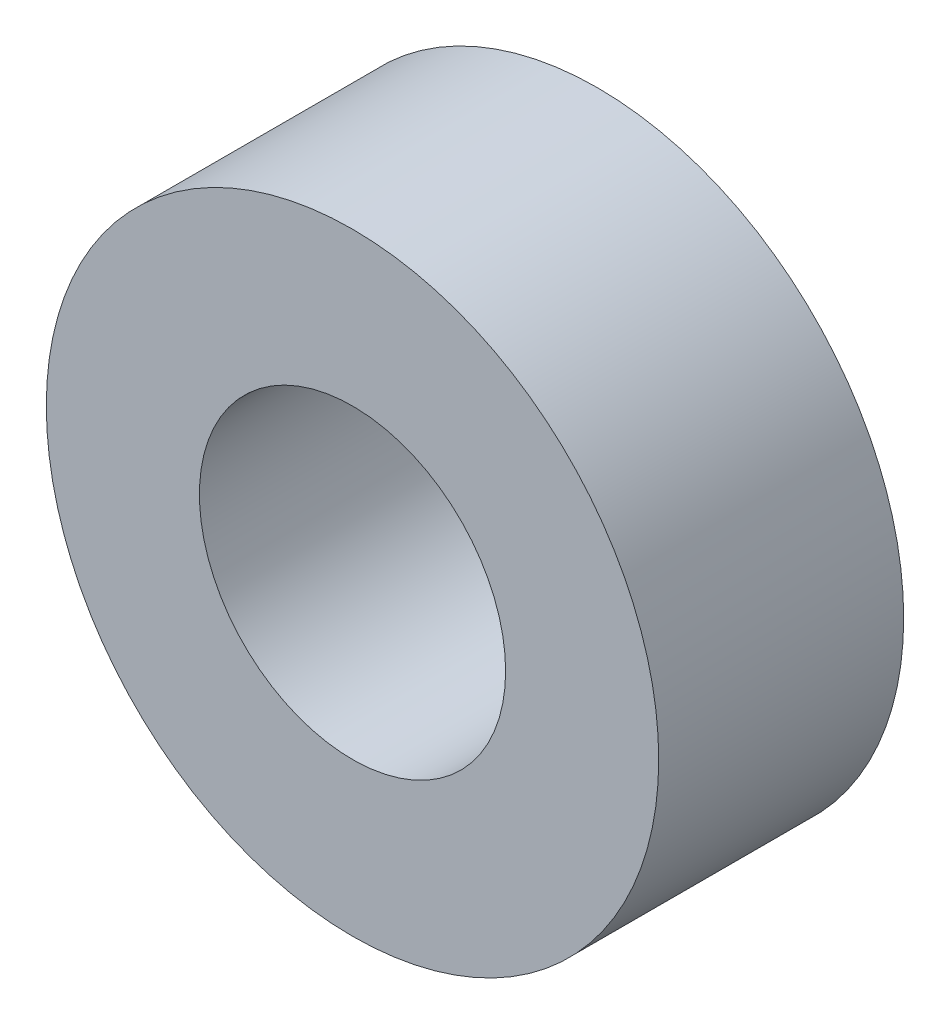
SolidWorks part; units mm, degrees
ref_plane "Front Plane" through (0, 0, 0) normal (0, 0, 1) x (1, 0, 0)
ref_plane "Top Plane" through (0, 0, 0) normal (0, 1, 0) x (1, 0, 0)
ref_plane "Right Plane" through (0, 0, 0) normal (1, 0, 0) x (0, 0, -1)
sketch "Sketch1" plane through (0, 0, 0) normal (0, 0, 1) x (1, 0, 0)
  circle A0 centre (0, 0) radius 2.5
  circle A1 centre (0, 0) radius 5
  dimension "D1" = 5
  dimension "D2" = 10
extrude "Boss-Extrude1" add sketch "Sketch1" along normal blind 4
